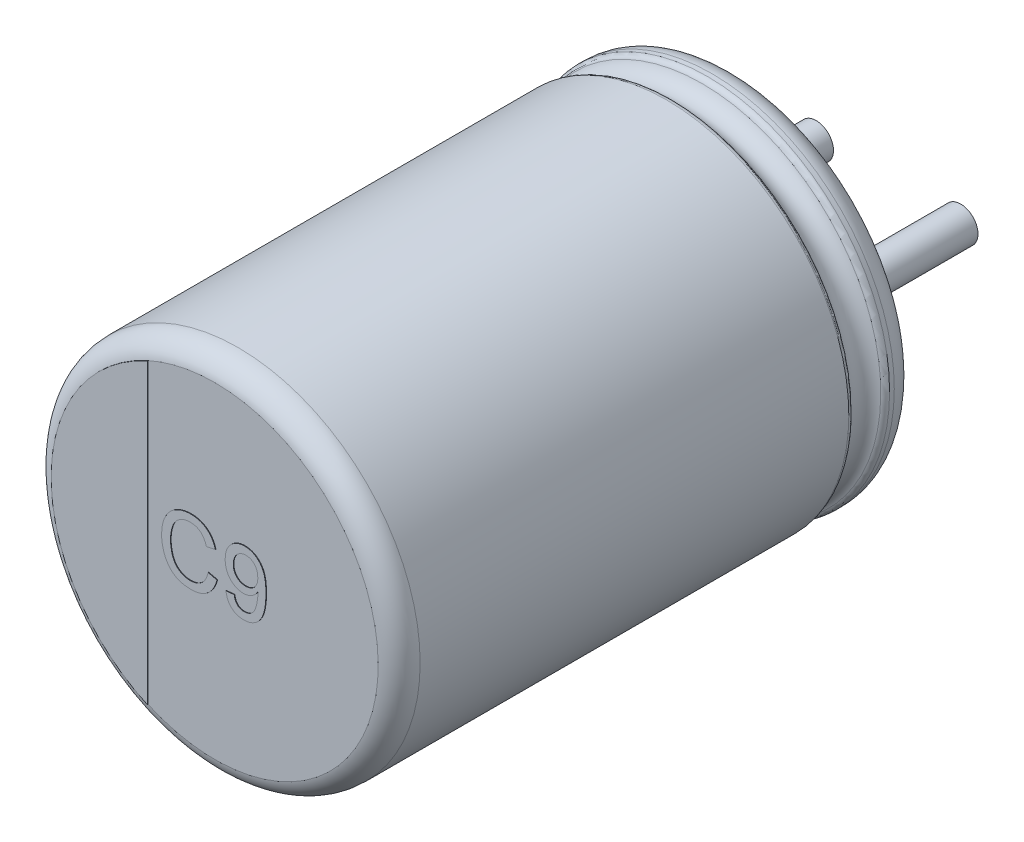
SolidWorks part; units mm, degrees
ref_plane "Plan de face" through (0, 0, 0) normal (0, 0, 1) x (1, 0, 0)
ref_plane "Plan de dessus" through (0, 0, 0) normal (0, 1, 0) x (1, 0, 0)
ref_plane "Plan de droite" through (0, 0, 0) normal (1, 0, 0) x (0, 0, -1)
sketch "Sketch10" plane through (0, 0, 0) normal (1, 0, 0) x (0, 0, -1)
  line L0 (18.1631, 0) -> (-18.9631, 0) construction
  line L1 (-9, 0) -> (-0.05, 0)
  line L2 (-9, 0) -> (-9, 2.8236)
  line L3 (-8.6, 3.15) -> (-1.1846, 3.15)
  line L4 (-0.05, 2.5531) -> (-0.05, 0)
  line L7 (-0.4794, 3.15) -> (-0.3982, 3.15)
  arc A0 (-9, 2.8236) -> (-8.6, 3.15) centre (-8.6068, 2.7501) cw
  arc A1 (-0.3982, 3.15) -> (-0.05, 2.5531) centre (-0.3982, 2.75) cw
  arc A2 (-0.5713, 3.0894) -> (-1.0926, 3.0894) centre (-0.832, 3.201) cw
  arc A3 (-1.0926, 3.0894) -> (-1.1846, 3.15) centre (-1.1846, 3.05) ccw
  arc A4 (-0.5713, 3.0894) -> (-0.4794, 3.15) centre (-0.4794, 3.05) cw
  point P4 (0.57, 0)
  point P13 (-9, 3.15)
  dimension "D2" = 0.4
  dimension "D3" = 0.4
  dimension "D4" = 0.1
  dimension "D5" = 0.1
  dimension "D1" = 3.15
  dimension "D7" = 0.05
  dimension "D8" = 3.15
revolve "Повернуть1" add sketch "Sketch10" angle 360 about L0
sketch "Эскиз2" plane through (0, 0, 0.05) normal (0, 0, -1) x (-1, 0, 0)
  line L1 (0, 0.7993) -> (0, -1.0496) construction
  line L2 (-1.25, 0) -> (3.6313, 0) construction
  circle A3 centre (-1.25, 0) radius 0.3
  circle A7 centre (1.25, 0) radius 0.3
  dimension "D1" = 2.5
extrude "Бобышка-Вытянуть1" add sketch "Эскиз2" along normal blind 2.7
sketch "Эскиз4" plane through (0, 0, 9) normal (0, 0, 1) x (1, 0, 0)
  line L0 (-1.1603, -2.5741) -> (-1.1603, 2.5741)
  circle A1 centre (0, 0) radius 2.8236 construction
  arc A2 (-1.1603, 2.5741) -> (-1.1603, -2.5741) centre (0, 0) ccw
extrude "Бобышка-Вытянуть2" add sketch "Эскиз4" along normal blind 0.01
sketch "Эскиз5" plane through (0, 0, 9) normal (0, 0, 1) x (1, 0, 0)
  text T0 "C9" font "Arial" height 1.1
extrude "Текст" add sketch "Эскиз5" along normal blind 0.01
sketch "Эскиз6" plane through (0, 0, 0.05) normal (0, 0, -1) x (-1, 0, 0)
  line L0 (-1.25, 0.4) -> (-1.6248, 0.4)
  line L1 (-1.25, -0.4) -> (-1.6248, -0.4)
  line L2 (1.25, -0.4) -> (1.6248, -0.4)
  line L3 (1.25, 0.4) -> (1.6248, 0.4)
  arc A0 (-1.8569, -0.7429) -> (1.8569, -0.7429) centre (0, 0) ccw
  arc A1 (-1.25, -0.4) -> (-1.25, 0.4) centre (-1.25, 0) ccw
  arc A2 (1.25, 0.4) -> (1.25, -0.4) centre (1.25, 0) ccw
  arc A3 (1.8569, 0.7429) -> (-1.8569, 0.7429) centre (0, 0) ccw
  arc A4 (1.6248, 0.4) -> (1.8569, 0.7429) centre (1.6248, 0.65) ccw
  arc A5 (1.6248, -0.4) -> (1.8569, -0.7429) centre (1.6248, -0.65) cw
  arc A6 (-1.8569, -0.7429) -> (-1.6248, -0.4) centre (-1.6248, -0.65) cw
  arc A7 (-1.6248, 0.4) -> (-1.8569, 0.7429) centre (-1.6248, 0.65) cw
  point P7 (1.9596, 0.4)
  point P23 (0, -2)
  point P24 (0, 2)
  dimension "D1" = 0.25
  dimension "D2" = 4
extrude "Бобышка-Вытянуть5" add sketch "Эскиз6" along normal blind 0.05 contours A3 A7 L0 A1 L1 A6 A0 A5 L2 A2 L3 A4
